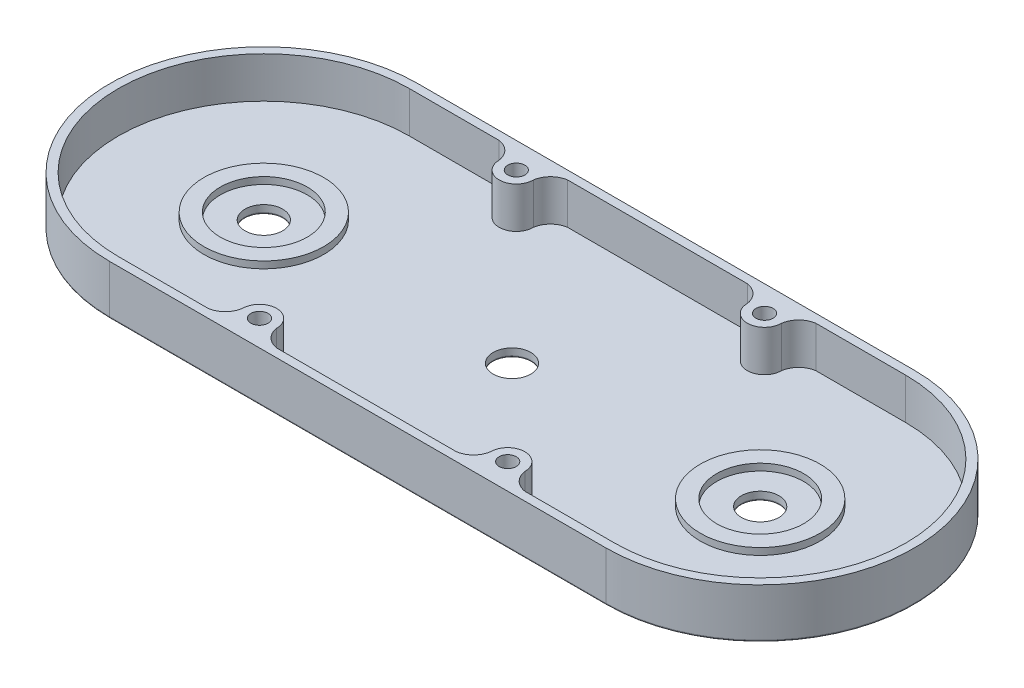
SolidWorks part; units mm, degrees
ref_plane "Front Plane" through (0, 0, 0) normal (0, 0, 1) x (1, 0, 0)
ref_plane "Top Plane" through (0, 0, 0) normal (0, 1, 0) x (1, 0, 0)
ref_plane "Right Plane" through (0, 0, 0) normal (1, 0, 0) x (0, 0, -1)
sketch "Sketch1" plane through (0, 0, 0) normal (0, 1, 0) x (1, 0, 0)
  line L0 (0, 45) -> (145, 45)
  line L1 (0, -45) -> (145, -45)
  arc A2 (0, 45) -> (0, -45) centre (0, 0) ccw
  arc A3 (145, -45) -> (145, 45) centre (145, 0) ccw
  circle A5 centre (0, 0) radius 20 construction
  circle A6 centre (145, 0) radius 20 construction
  dimension "D2" = 2
extrude "Boss-Extrude1" add sketch "Sketch1" along normal blind 14.5
sketch "Sketch2" plane through (0, 14.5, 0) normal (0, 1, 0) x (1, 0, 0)
  line L7 (145, 42.5) -> (0, 42.5)
  line L8 (0, -42.5) -> (145, -42.5)
  line L9 (145, 42.5) -> (0, 42.5)
  line L10 (0, -42.5) -> (145, -42.5)
  arc A7 (145, -42.5) -> (145, 42.5) centre (145, 0) ccw
  arc A8 (0, 42.5) -> (0, -42.5) centre (0, 0) ccw
  arc A9 (145, -42.5) -> (145, 42.5) centre (145, 0) ccw
  arc A10 (0, 42.5) -> (0, -42.5) centre (0, 0) ccw
  dimension "D1" = 2.5
extrude "Cut-Extrude1" cut sketch "Sketch2" against normal blind 12
sketch "Sketch3" plane through (0, 2.5, 0) normal (0, 1, 0) x (1, 0, 0)
  circle A1 centre (0, 0) radius 12.7
  circle A2 centre (0, 0) radius 17.5
  circle A3 centre (145, 0) radius 17.5
  circle A4 centre (145, 0) radius 12.7
  dimension "D1" = 2
  dimension "D2" = 25.4
extrude "Boss-Extrude2" add sketch "Sketch3" along normal blind 2
sketch "Sketch4" plane through (0, 2.5, 0) normal (0, 1, 0) x (1, 0, 0)
  line L0 (0, 0) -> (72.5, 0) construction
  circle A0 centre (72.5, 0) radius 5.5
extrude "Cut-Extrude2" cut sketch "Sketch4" against normal through all
sketch "Sketch5" plane through (0, 2.5, 0) normal (0, 1, 0) x (1, 0, 0)
  line L0 (108.75, 0) -> (108.75, 42.5) construction
  line L1 (145, 42.5) -> (0, 42.5) construction
  line L3 (0, 0) -> (145, 0) construction
  circle A0 centre (0, 0) radius 36.25 construction
  circle A1 centre (145, 0) radius 36.25 construction
  circle A2 centre (72.5, 0) radius 36.25
  arc A3 (103.75, 37.5) -> (113.75, 37.5) centre (108.75, 37.5) ccw
  arc A4 (113.75, 37.5) -> (118.75, 42.5) centre (119.6325, 36.6175) cw
  arc A5 (103.75, 37.5) -> (98.75, 42.5) centre (97.8675, 36.6175) ccw
  arc A6 (41.25, 37.5) -> (46.25, 42.5) centre (47.1325, 36.6175) cw
  arc A7 (31.25, 37.5) -> (41.25, 37.5) centre (36.25, 37.5) ccw
  arc A8 (31.25, 37.5) -> (26.25, 42.5) centre (25.3675, 36.6175) ccw
  arc A9 (31.25, -37.5) -> (26.25, -42.5) centre (25.3675, -36.6175) cw
  arc A10 (31.25, -37.5) -> (41.25, -37.5) centre (36.25, -37.5) cw
  arc A11 (41.25, -37.5) -> (46.25, -42.5) centre (47.1325, -36.6175) ccw
  arc A12 (103.75, -37.5) -> (98.75, -42.5) centre (97.8675, -36.6175) cw
  arc A13 (103.75, -37.5) -> (113.75, -37.5) centre (108.75, -37.5) cw
  arc A14 (113.75, -37.5) -> (118.75, -42.5) centre (119.6325, -36.6175) ccw
  dimension "D1" = 2
  dimension "D2" = 10
  dimension "D3" = 0
  dimension "D4" = 2
extrude "Boss-Extrude4" add sketch "Sketch5" along normal blind 12 contours A5 A3 A4 A7 | A8 A7 A6 | A11 A10 A9 L3 | A14 A13 A12 L3
sketch "Sketch6" plane through (0, 14.5, 0) normal (0, 1, 0) x (1, 0, 0)
  line L0 (0, 0) -> (145, 0) construction
  circle A0 centre (108.7546, 37.5122) radius 5.0131
  circle A1 centre (108.7546, 37.5122) radius 2.5
  circle A2 centre (36.2546, 37.5122) radius 5.0131
  circle A3 centre (36.2546, 37.5122) radius 2.5
  circle A4 centre (36.2546, -37.5122) radius 5.0131
  circle A5 centre (36.2546, -37.5122) radius 2.5
  circle A6 centre (108.7546, -37.5122) radius 5.0131
  circle A7 centre (108.7546, -37.5122) radius 2.5
  dimension "D1" = 2
extrude "Cut-Extrude4" cut sketch "Sketch6" against normal blind 10 contours A1 | A3 | A5 | A7
sketch "Sketch7" plane through (0, 2.5, 0) normal (0, 1, 0) x (1, 0, 0)
  circle A0 centre (0, 0) radius 5.5
  circle A1 centre (145, 0) radius 5.5
  dimension "D1" = 2
extrude "Cut-Extrude5" cut sketch "Sketch7" against normal blind 10
fillet "Fillet1" radius 0.5 7 edges at (72.5, 0, 45) (190, 0, 0) (72.5, 0, -45) (-45, 0, 0) (72.5, 0, 5.5) (145, 0, 5.5) (0, 0, 5.5)
